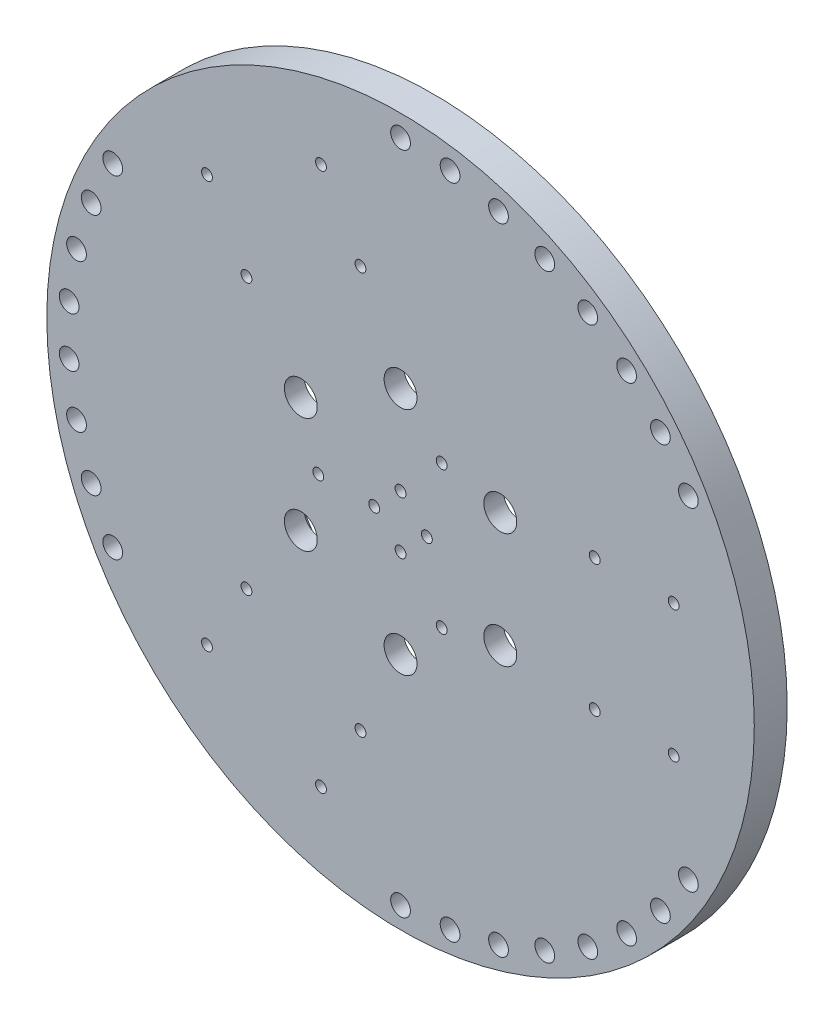
SolidWorks part; units mm, degrees
material "1060 Alloy"
ref_plane "Front Plane" through (0, 0, 0) normal (0, 0, 1) x (1, 0, 0)
ref_plane "Top Plane" through (0, 0, 0) normal (0, 1, 0) x (1, 0, 0)
ref_plane "Right Plane" through (0, 0, 0) normal (1, 0, 0) x (0, 0, -1)
sketch "Sketch1" plane through (0, 0, 0) normal (0, 0, 1) x (1, 0, 0)
  line L0 (0, -125.7103) -> (0, 128.6807) construction
  line L1 (-162.8772, -94.0372) -> (162.8772, 94.0372) construction
  line L2 (195.1309, -112.6589) -> (-195.1309, 112.6589) construction
  circle A0 centre (0, 0) radius 107.5
  circle A1 centre (0, 0) radius 101 construction
  circle A2 centre (0, 0) radius 94
  point P7 (122.7223, 224.7398)
  point P10 (0, 0)
  point P13 (0, 0)
  dimension "D1" = 60
  dimension "D2" = 60
extrude "Boss-Extrude1" add sketch "Sketch1" along normal blind 10 contours A2 | A0 A2
sketch "Sketch2" plane through (0, 0, 10) normal (0, 0, 1) x (1, 0, 0)
  line L0 (0, 0) -> (0, 94) construction
  line L1 (88, 25) -> (88, -25)
  line L2 (0, 25) -> (90.6146, 25)
  line L3 (54, 25) -> (54, -25)
  line L4 (0, -25) -> (90.6146, -25)
  line L5 (0, 0) -> (0, 88) construction
  line L6 (-22.3494, -88.7102) -> (-65.6506, -63.7102)
  line L7 (21.6506, -12.5) -> (-23.6566, -90.9745)
  line L8 (0, 0) -> (-62.377, 108.0401) construction
  line L9 (-48.6506, 34.2654) -> (-5.3494, 59.2654)
  line L10 (-21.6506, -12.5) -> (-66.9579, 65.9745)
  line L11 (21.6506, 12.5) -> (-23.6566, 90.9745)
  line L12 (-65.6506, 63.7102) -> (-22.3494, 88.7102)
  line L13 (-5.3494, -59.2654) -> (-48.6506, -34.2654)
  line L14 (-21.6506, 12.5) -> (-66.9579, -65.9745)
  circle A0 centre (0, 0) radius 101 construction
  circle A1 centre (0, 0) radius 94
  circle A2 centre (0, 0) radius 35 construction
  circle A4 centre (0, 0) radius 25 construction
  circle A5 centre (0, 0) radius 8 construction
  point P4 (-94.0182, -36.8994)
  point P5 (0, 101)
  point P6 (87.4686, -50.5)
  point P7 (0, 0)
  point P9 (0, 0)
  point P10 (-87.4686, -50.5)
  point P12 (-98.4677, -22.4746)
  point P13 (0, 0)
  point P14 (15.0533, 99.8719)
  point P15 (29.7703, 96.5129)
  point P16 (43.8223, 90.9979)
  point P17 (56.8953, 83.4501)
  point P18 (68.6974, 74.0382)
  point P19 (78.965, 62.9725)
  point P20 (87.4686, 50.5)
  point P21 (0, 0)
  point P22 (-100.7176, -7.5477)
  point P23 (-100.7176, 7.5477)
  point P24 (78.965, -62.9725)
  point P25 (68.6974, -74.0382)
  point P26 (56.8953, -83.4501)
  point P27 (43.8223, -90.9979)
  point P28 (29.7703, -96.5129)
  point P29 (15.0533, -99.8719)
  point P30 (0, -101)
  point P31 (0, 0)
  point P32 (-98.4677, 22.4746)
  point P33 (-94.0182, 36.8994)
  point P34 (-87.4686, 50.5)
  point P35 (0, 0)
  point P45 (0, 88)
  point P52 (0, 35)
  point P62 (0, 0)
  point P64 (30.3109, 17.5)
  point P65 (30.3109, -17.5)
  point P66 (0, -35)
  point P67 (-30.3109, -17.5)
  point P68 (-30.3109, 17.5)
  point P69 (0, 0)
  point P70 (0, 8)
  point P71 (12.5, 21.6506)
  point P74 (12.5, -21.6506)
  point P75 (-25, 0)
  point P76 (0, 0)
  point P78 (8, 0)
  point P79 (0, -8)
  point P80 (-8, 0)
  point P81 (0, 0)
  point P90 (-46.8205, 41.0955)
  point P91 (-58.8205, 61.8801)
  point P92 (-12.1795, 61.0955)
  point P93 (-24.1795, 81.8801)
  point P94 (0, 0)
  point P95 (59, 20)
  point P96 (83, 20)
  point P97 (59, -20)
  point P98 (83, -20)
  point P99 (-12.1795, -61.0955)
  point P100 (-24.1795, -81.8801)
  point P101 (-46.8205, -41.0955)
  point P102 (-58.8205, -61.8801)
  point P103 (0, 0)
  point P111 (0, 0)
  dimension "D1" = 8
  dimension "D17" = 6
  dimension "D18" = 3
  dimension "D19" = 4
  dimension "D2" = 8
  dimension "D6" = 34
  dimension "D7" = 24
  dimension "D8" = 40
  dimension "D9" = 40
  dimension "D10" = 40
  dimension "D11" = 3
  dimension "D20" = 30
  dimension "D4" = 25
  dimension "D5" = 25
  dimension "D3" = 8
  dimension "D22" = 3
hole_wizard "Ø10.0 (10) Diameter Hole1" positions "Sketch3" profile "Sketch4" hole size "Ø10.0" standard "ISO" end condition through all
sketch "Sketch3" plane through (0, 0, 10) normal (0, 0, 1) x (1, 0, 0)
  point P0 (-30.3109, 17.5)
  point P3 (-30.3109, -17.5)
  point P6 (0, -35)
  point P9 (30.3109, -17.5)
  point P12 (30.3109, 17.5)
  point P15 (0, 35)
sketch "Sketch4" plane through (-30.3109, 17.5, 10) normal (1, 0, 0) x (0, -1, 0)
  line L0 (0, 0) -> (0, 10)
  line L1 (0, 10) -> (5, 10)
  line L2 (5, 10) -> (5, 0)
  line L5 (5, 0) -> (0, 0)
  line L11 (0, -6.35) -> (0, 107.95) construction
  dimension "Thru Hole Dia." = 10
  dimension "Thru Hole Depth" = 10
hole_wizard "Ø6.0 (6) Diameter Hole1" positions "Sketch11" profile "Sketch12" hole size "Ø6.0" standard "ISO" end condition through all
sketch "Sketch11" plane through (0, 0, 10) normal (0, 0, 1) x (1, 0, 0)
  point P0 (-87.4686, -50.5)
  point P3 (-94.0182, -36.8994)
  point P6 (-98.4677, -22.4746)
  point P9 (-100.7176, -7.5477)
  point P12 (-100.7176, 7.5477)
  point P15 (-98.4677, 22.4746)
  point P18 (-94.0182, 36.8994)
  point P21 (-87.4686, 50.5)
  point P24 (0, 101)
  point P27 (15.0533, 99.8719)
  point P30 (29.7703, 96.5129)
  point P33 (43.8223, 90.9979)
  point P36 (56.8953, 83.4501)
  point P39 (68.6974, 74.0382)
  point P42 (78.965, 62.9725)
  point P45 (87.4686, 50.5)
  point P48 (87.4686, -50.5)
  point P51 (78.965, -62.9725)
  point P54 (68.6974, -74.0382)
  point P57 (56.8953, -83.4501)
  point P60 (43.8223, -90.9979)
  point P63 (29.7703, -96.5129)
  point P66 (15.0533, -99.8719)
  point P69 (0, -101)
sketch "Sketch12" plane through (-87.4686, -50.5, 10) normal (1, 0, 0) x (0, -1, 0)
  line L0 (0, 0) -> (0, 10)
  line L1 (0, 10) -> (3, 10)
  line L2 (3, 10) -> (3, 0)
  line L5 (3, 0) -> (0, 0)
  line L11 (0, -6.35) -> (0, 107.95) construction
  dimension "Thru Hole Dia." = 6
  dimension "Thru Hole Depth" = 10
hole_wizard "M4 Tapped Hole2" positions "Sketch13" profile "Sketch14" tap size "M4" standard "ISO" end condition through all
sketch "Sketch13" plane through (0, 0, 10) normal (0, 0, 1) x (1, 0, 0)
  point P0 (-58.8205, 61.8801)
  point P3 (-24.1795, 81.8801)
  point P6 (-12.1795, 61.0955)
  point P9 (-46.8205, 41.0955)
  point P12 (12.5, 21.6506)
  point P15 (-25, 0)
  point P18 (12.5, -21.6506)
  point P21 (59, 20)
  point P24 (83, 20)
  point P27 (59, -20)
  point P30 (83, -20)
  point P33 (-12.1795, -61.0955)
  point P36 (-46.8205, -41.0955)
  point P39 (-58.8205, -61.8801)
  point P42 (-24.1795, -81.8801)
  point P46 (-8, 0)
  point P49 (0, 8)
  point P52 (8, 0)
  point P55 (0, -8)
sketch "Sketch14" plane through (-58.8205, 61.8801, 10) normal (1, 0, 0) x (0, -1, 0)
  line L0 (0, 0) -> (0, 10)
  line L1 (0, 10) -> (1.65, 10)
  line L2 (1.65, 10) -> (1.65, 0)
  line L5 (1.65, 0) -> (0, 0)
  line L11 (0, -6.35) -> (0, 107.95) construction
  dimension "Thru Tap Drill Dia." = 3.3
  dimension "Thru Tap Drill Depth" = 10
cosmetic thread "Hole Thread20" parameters "D2"=4
cosmetic thread "Hole Thread21" parameters "D2"=4
cosmetic thread "Hole Thread22" parameters "D2"=4
cosmetic thread "Hole Thread23" parameters "D2"=4
cosmetic thread "Hole Thread24" parameters "D2"=4
cosmetic thread "Hole Thread25" parameters "D2"=4
cosmetic thread "Hole Thread26" parameters "D2"=4
cosmetic thread "Hole Thread27" parameters "D2"=4
cosmetic thread "Hole Thread28" parameters "D2"=4
cosmetic thread "Hole Thread29" parameters "D2"=4
cosmetic thread "Hole Thread30" parameters "D2"=4
cosmetic thread "Hole Thread31" parameters "D2"=4
cosmetic thread "Hole Thread32" parameters "D2"=4
cosmetic thread "Hole Thread33" parameters "D2"=4
cosmetic thread "Hole Thread34" parameters "D2"=4
cosmetic thread "Hole Thread35" parameters "D2"=4
cosmetic thread "Hole Thread36" parameters "D2"=4
cosmetic thread "Hole Thread37" parameters "D2"=4
cosmetic thread "Hole Thread38" parameters "D2"=4
sketch "Sketch15" plane through (0, 0, 0) normal (0, 0, -1) x (-1, 0, 0)
  circle A0 centre (0, 0) radius 45
extrude "Cut-Extrude1" cut sketch "Sketch15" against normal blind 4
sketch "Sketch16" plane through (0, 0, 4) normal (0, 0, -1) x (-1, 0, 0)
  circle A0 centre (0, 0) radius 15
extrude "Cut-Extrude2" cut sketch "Sketch16" against normal blind 2
